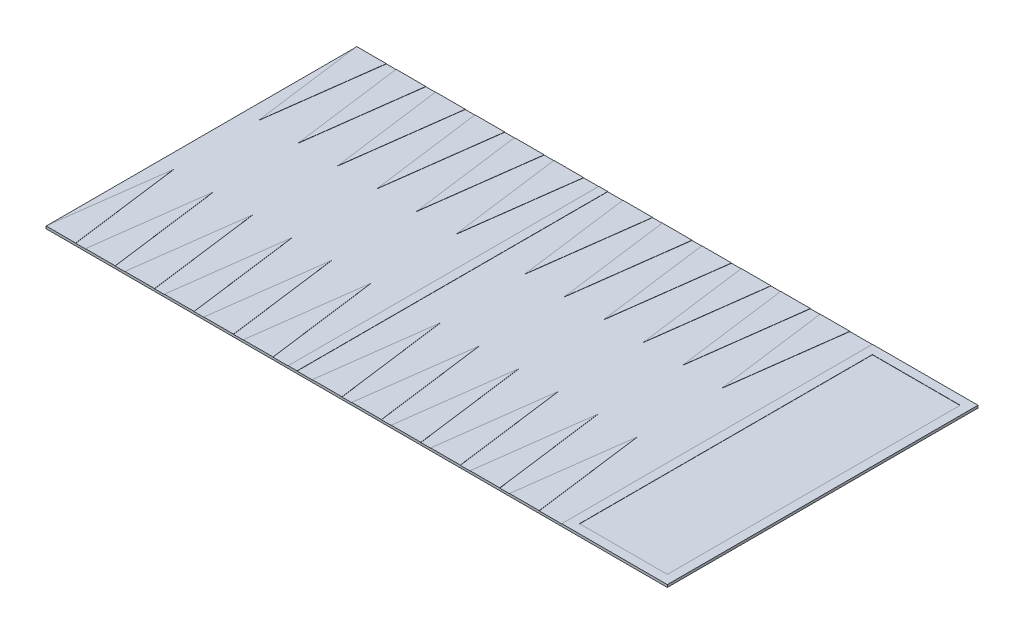
SolidWorks part; units mm, degrees
ref_plane "Front Plane" through (0, 0, 0) normal (0, 0, 1) x (1, 0, 0)
ref_plane "Top Plane" through (0, 0, 0) normal (0, 1, 0) x (1, 0, 0)
ref_plane "Right Plane" through (0, 0, 0) normal (1, 0, 0) x (0, 0, -1)
sketch "Sketch1" plane through (0, 0, 0) normal (0, 1, 0) x (1, 0, 0)
  line L1 (-350, -175) -> (350, -175)
  line L2 (-350, -175) -> (-350, 175)
  line L3 (-350, 175) -> (350, 175)
  line L4 (350, -175) -> (350, 175)
  line L5 (-350, -175) -> (350, 175) construction
  line L6 (-350, 175) -> (350, -175) construction
  point P0 (0, 0)
  dimension "D1" = 700
  dimension "D2" = 350
extrude "Boss-Extrude1" add sketch "Sketch1" along normal blind 2.54
sketch "Sketch2" plane through (0, 2.54, 0) normal (0, 1, 0) x (1, 0, 0)
  line L0 (275, 175) -> (275, -175) construction
  line L1 (350, 175) -> (-350, 175) construction
  line L2 (-350, -175) -> (350, -175) construction
  line L3 (350, -175) -> (350, 175) construction
  line L4 (-350, 175) -> (-333.2801, 48)
  line L5 (-333.2801, 48) -> (-316.5603, 175)
  line L6 (-333.2801, 48) -> (-333.2801, 175) construction
  line L7 (-350, 175) -> (-316.5603, 175)
  line L23 (-305.55, 175) -> (-272.1103, 175)
  line L24 (-288.8301, 48) -> (-272.1103, 175)
  line L25 (-305.55, 175) -> (-288.8301, 48)
  line L26 (-261.1, 175) -> (-227.6603, 175)
  line L27 (-244.3801, 48) -> (-227.6603, 175)
  line L28 (-261.1, 175) -> (-244.3801, 48)
  line L29 (-216.65, 175) -> (-183.2103, 175)
  line L30 (-199.9301, 48) -> (-183.2103, 175)
  line L31 (-216.65, 175) -> (-199.9301, 48)
  line L32 (-172.2, 175) -> (-138.7603, 175)
  line L33 (-155.4801, 48) -> (-138.7603, 175)
  line L34 (-172.2, 175) -> (-155.4801, 48)
  line L35 (-127.75, 175) -> (-94.3103, 175)
  line L36 (-111.0301, 48) -> (-94.3103, 175)
  line L37 (-127.75, 175) -> (-111.0301, 48)
  line L38 (-350, 0) -> (350, 0) construction
  line L39 (-350, 175) -> (-350, -175) construction
  line L40 (-333.2801, -48) -> (-333.2801, -175) construction
  line L41 (-127.75, -175) -> (-111.0301, -48)
  line L42 (-111.0301, -48) -> (-94.3103, -175)
  line L43 (-127.75, -175) -> (-94.3103, -175)
  line L44 (-172.2, -175) -> (-155.4801, -48)
  line L45 (-155.4801, -48) -> (-138.7603, -175)
  line L46 (-172.2, -175) -> (-138.7603, -175)
  line L47 (-216.65, -175) -> (-199.9301, -48)
  line L48 (-199.9301, -48) -> (-183.2103, -175)
  line L49 (-216.65, -175) -> (-183.2103, -175)
  line L50 (-261.1, -175) -> (-244.3801, -48)
  line L51 (-244.3801, -48) -> (-227.6603, -175)
  line L52 (-261.1, -175) -> (-227.6603, -175)
  line L53 (-305.55, -175) -> (-288.8301, -48)
  line L54 (-288.8301, -48) -> (-272.1103, -175)
  line L55 (-305.55, -175) -> (-272.1103, -175)
  line L56 (-350, -175) -> (-316.5603, -175)
  line L57 (-333.2801, -48) -> (-316.5603, -175)
  line L58 (-350, -175) -> (-333.2801, -48)
  line L59 (-50.026, 175) -> (-33.3061, 48)
  line L60 (-33.3061, 48) -> (-16.5863, 175)
  line L61 (-50.026, 175) -> (-16.5863, 175)
  line L62 (-5.576, 175) -> (27.8637, 175)
  line L63 (11.1439, 48) -> (27.8637, 175)
  line L64 (-5.576, 175) -> (11.1439, 48)
  line L65 (38.874, 175) -> (72.3137, 175)
  line L66 (55.5939, 48) -> (72.3137, 175)
  line L67 (38.874, 175) -> (55.5939, 48)
  line L68 (83.324, 175) -> (116.7637, 175)
  line L69 (100.0439, 48) -> (116.7637, 175)
  line L70 (83.324, 175) -> (100.0439, 48)
  line L71 (127.774, 175) -> (161.2137, 175)
  line L72 (144.4939, 48) -> (161.2137, 175)
  line L73 (127.774, 175) -> (144.4939, 48)
  line L74 (172.224, 175) -> (205.6637, 175)
  line L75 (188.9439, 48) -> (205.6637, 175)
  line L76 (172.224, 175) -> (188.9439, 48)
  line L77 (172.224, -175) -> (188.9439, -48)
  line L78 (188.9439, -48) -> (205.6637, -175)
  line L79 (172.224, -175) -> (205.6637, -175)
  line L80 (127.774, -175) -> (144.4939, -48)
  line L81 (144.4939, -48) -> (161.2137, -175)
  line L82 (127.774, -175) -> (161.2137, -175)
  line L83 (83.324, -175) -> (100.0439, -48)
  line L84 (100.0439, -48) -> (116.7637, -175)
  line L85 (83.324, -175) -> (116.7637, -175)
  line L86 (38.874, -175) -> (55.5939, -48)
  line L87 (55.5939, -48) -> (72.3137, -175)
  line L88 (38.874, -175) -> (72.3137, -175)
  line L89 (-5.576, -175) -> (11.1439, -48)
  line L90 (11.1439, -48) -> (27.8637, -175)
  line L91 (-5.576, -175) -> (27.8637, -175)
  line L92 (-50.026, -175) -> (-16.5863, -175)
  line L93 (-33.3061, -48) -> (-16.5863, -175)
  line L94 (-50.026, -175) -> (-33.3061, -48)
  line L95 (-33.3061, 48) -> (-33.3061, 175) construction
  line L96 (-33.3061, -48) -> (-33.3061, -175) construction
  line L97 (-94.3103, 175) -> (-50.026, 175) construction
  line L98 (-77.1681, -175) -> (-67.1681, -175)
  line L99 (-77.1681, -175) -> (-77.1681, 175)
  line L100 (-77.1681, 175) -> (-67.1681, 175)
  line L101 (-67.1681, -175) -> (-67.1681, 175)
  line L102 (-77.1681, -175) -> (-67.1681, 175) construction
  line L103 (-77.1681, 175) -> (-67.1681, -175) construction
  line L105 (231.0637, -175) -> (241.0637, -175)
  line L106 (231.0637, -175) -> (231.0637, 175)
  line L107 (231.0637, 175) -> (241.0637, 175)
  line L108 (241.0637, -175) -> (241.0637, 175)
  line L109 (231.0637, -175) -> (241.0637, 175) construction
  line L110 (231.0637, 175) -> (241.0637, -175) construction
  line L111 (241.0637, 175) -> (350, 175)
  line L112 (241.0637, 175) -> (241.0637, 165)
  line L113 (241.0637, 165) -> (350, 165)
  line L114 (350, 175) -> (350, 165)
  line L115 (241.0637, -175) -> (350, -175)
  line L116 (241.0637, -175) -> (241.0637, -165)
  line L117 (241.0637, -165) -> (350, -165)
  line L118 (350, -175) -> (350, -165)
  line L119 (350, -165) -> (340, -165)
  line L120 (350, -165) -> (350, 165)
  line L121 (350, 165) -> (340, 165)
  line L122 (340, -165) -> (340, 165)
  point P51 (-72.1681, 0)
  point P94 (-72.1681, 175)
  point P95 (236.0637, 0)
  line M48 (350, -175) -> (350, 175)
  line M49 (350, 175) -> (-350, 175)
  line M51 (-350, -175) -> (350, -175)
  dimension "D1" = 75
  dimension "D2" = 7.5
  dimension "D3" = 127
  dimension "D6" = 10
  dimension "D7" = 10
  dimension "D8" = 10
  dimension "D9" = 10
  dimension "D10" = 10
  dimension "D11" = 25.4
  dimension "D4" = 6
  dimension "D5" = 2
extrude "Boss-Extrude2" add sketch "Sketch2" along normal blind 0.254 contours L4 L5 M49 | L25 L24 M49 | L28 L27 M49 | L31 L30 M49 | L34 L33 M49 | L37 L36 M49 | L101 L99 M51 M49 | L59 L60 M49 | L64 L63 M49 | L67 L66 M49 | L70 L69 M49 | L73 L72 M49 | L76 L75 M49 | L58 L57 M51 | L54 L53 M51 | L51 L50 M51 | L48 L47 M51 | L45 L44 M51 | L42 L41 M51 | L94 L93 M51 | L90 L89 M51 | L87 L86 M51 | L84 L83 M51 | L81 L80 M51 | L78 L77 M51 | L108 L106 M51 M49 | L117 L108 M51 M48 | L122 L117 L113 M48 | L108 L113 M48 M49
scale "Scale1" scale about centroid uniform scaling yes scale factor 1.5
